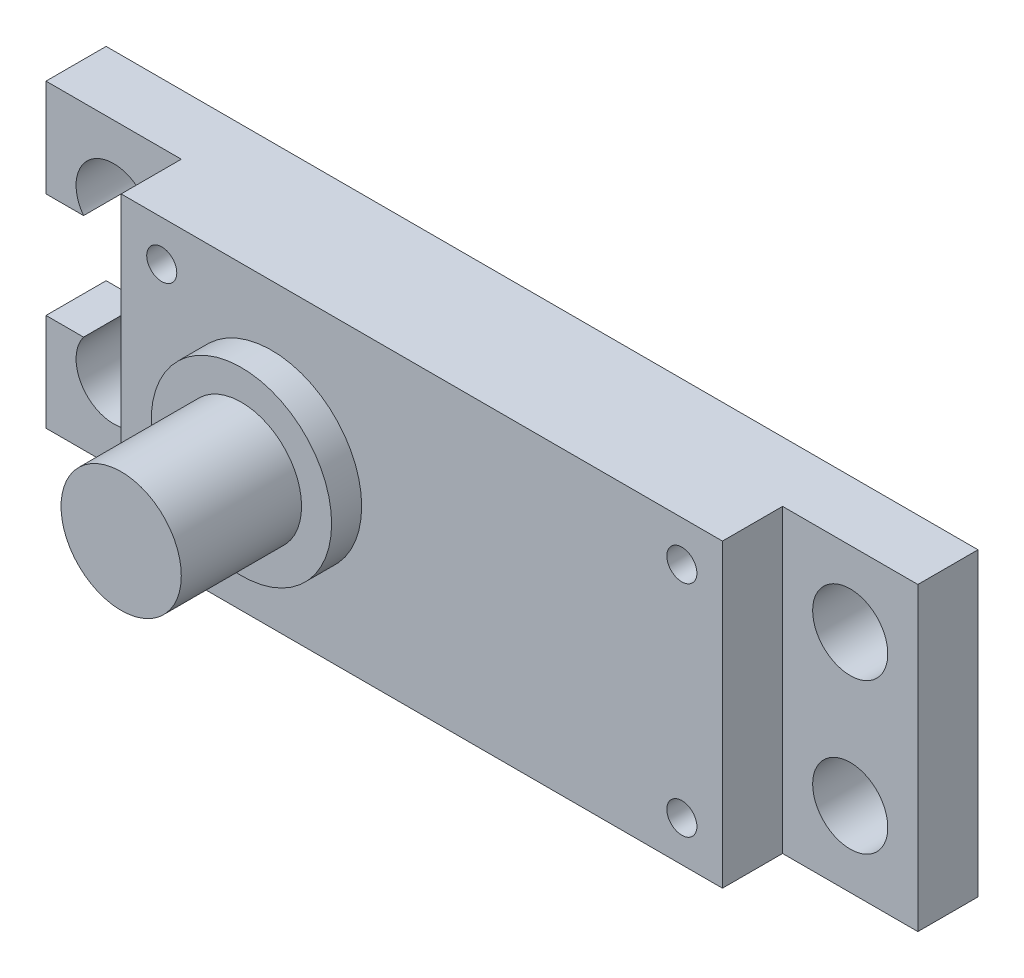
SolidWorks part; units mm, degrees
ref_plane "Face" through (0, 0, 0) normal (0, 0, 1) x (1, 0, 0)
ref_plane "Dessus" through (0, 0, 0) normal (0, 1, 0) x (1, 0, 0)
ref_plane "Droite" through (0, 0, 0) normal (1, 0, 0) x (0, 0, -1)
sketch "Esquisse1" plane through (0, 0, 0) normal (0, 0, 1) x (1, 0, 0)
  line L1 (0, 20) -> (58, 20)
  line L2 (0, 20) -> (0, 0)
  line L3 (0, 0) -> (58, 0)
  line L4 (58, 20) -> (58, 0)
  dimension "D1" = 20
  dimension "D2" = 58
extrude "Extrusion1" add sketch "Esquisse1" along normal blind 8
sketch "Esquisse2" plane through (0, 0, 0) normal (0, 0, -1) x (-1, 0, 0)
  line L0 (-60.8088, 10) -> (3.3885, 10) construction
  line L1 (-47.7, 18.7) -> (-10.3, 18.7)
  line L2 (-47.7, 18.7) -> (-47.7, 1.3)
  line L3 (-47.7, 1.3) -> (-10.3, 1.3)
  line L4 (-10.3, 18.7) -> (-10.3, 1.3)
  line L5 (-29, 26.2419) -> (-29, -6.2687) construction
  line L6 (-58, 0) -> (-58, 20) construction
  line L7 (0, 20) -> (0, 0) construction
  line L8 (-58, 20) -> (0, 20) construction
  line L9 (0, 0) -> (-58, 0) construction
  dimension "D1" = 37.4
  dimension "D2" = 17.4
extrude "Enlèv. mat.-Extru.1" cut sketch "Esquisse2" against normal blind 6
sketch "Esquisse3" plane through (0, 20, 0) normal (0, 1, 0) x (1, 0, 0)
  line L0 (29, 7.8921) -> (29, -24.2537) construction
  line L1 (58, -8) -> (58, 0) construction
  line L2 (0, -8) -> (0, 0) construction
  line L3 (58, 0) -> (0, 0) construction
  line L4 (9, -4) -> (0, -4)
  line L5 (9, -4) -> (9, -8)
  line L6 (9, -8) -> (0, -8)
  line L7 (0, -4) -> (0, -8)
  line L8 (58, -4) -> (58, -8)
  line L9 (49, -8) -> (58, -8)
  line L10 (49, -4) -> (49, -8)
  line L11 (49, -4) -> (58, -4)
  dimension "D1" = 4
  dimension "D2" = 40
extrude "Enlèv. mat.-Extru.2" cut sketch "Esquisse3" against normal through all
sketch "Esquisse4" plane through (0, 0, 0) normal (0, 0, -1) x (-1, 0, 0)
  line L0 (-29, 25.2889) -> (-29, -5.3683) construction
  line L1 (-64.7005, 10) -> (4.5905, 10) construction
  line L2 (0, 20) -> (0, 0) construction
  line L3 (-58, 0) -> (-58, 20) construction
  line L4 (-58, 20) -> (0, 20) construction
  line L5 (0, 0) -> (-58, 0) construction
  line L6 (-49, 0) -> (-49, 20) construction
  circle A0 centre (-53.5, 15) radius 2.5
  circle A1 centre (-46.3, 17.3) radius 1
  circle A2 centre (-46.3, 2.7) radius 1
  circle A3 centre (-53.5, 5) radius 2.5
  circle A4 centre (-4.5, 5) radius 2.5
  circle A5 centre (-11.7, 2.7) radius 1
  circle A6 centre (-11.7, 17.3) radius 1
  circle A7 centre (-4.5, 15) radius 2.5
  dimension "D1" = 5
  dimension "D2" = 2
  dimension "D3" = 4.5
  dimension "D4" = 2.7
  dimension "D5" = 10
  dimension "D6" = 14.6
extrude "Enlèv. mat.-Extru.3" cut sketch "Esquisse4" against normal through all
sketch "Esquisse5" plane through (0, 0, 8) normal (0, 0, 1) x (1, 0, 0)
  line L0 (3.4324, 10) -> (55.7935, 10) construction
  line L1 (9, 0) -> (49, 0) construction
  line L2 (49, 20) -> (9, 20) construction
  line L3 (9, 0) -> (9, 20) construction
  circle A0 centre (19, 10) radius 4
  dimension "D1" = 8
  dimension "D2" = 10
extrude "Extrusion2" add sketch "Esquisse5" along normal blind 10
sketch "Esquisse6" plane through (0, 0, 0) normal (0, 0, -1) x (-1, 0, 0)
  line L0 (-28.8333, 10) -> (7.867, 10) construction
  line L1 (-58, 20) -> (0, 20) construction
  line L2 (0, 0) -> (-58, 0) construction
  line L3 (0, 20) -> (0, 0) construction
  line L4 (-10.3, 13.5) -> (0, 13.5)
  line L5 (-10.3, 13.5) -> (-10.3, 6.5)
  line L6 (-10.3, 6.5) -> (0, 6.5)
  line L7 (0, 13.5) -> (0, 6.5)
  line L8 (-10.3, 1.3) -> (-10.3, 18.7) construction
  dimension "D1" = 7
extrude "Enlèv. mat.-Extru.4" cut sketch "Esquisse6" against normal up to surface (4 mm away) up to face at (2, 15, 4)
sketch "Esquisse10" plane through (0, 20, 0) normal (0, 1, 0) x (1, 0, 0)
  line L0 (10.3, -6) -> (47.7, -6) construction
  line L1 (10.3, -6) -> (47.7, -6)
  line L2 (10.3, -6) -> (10.3, -6.5)
  line L3 (10.3, -6.5) -> (47.7, -6.5)
  line L4 (47.7, -6) -> (47.7, -6.5)
  line L5 (47.7, -6) -> (47.7, 0) construction
  line L6 (10.3, -6) -> (10.3, 0) construction
  dimension "D1" = 0.5
extrude "Extrusion8" add sketch "Esquisse10" against normal up to surface (20 mm away) up to face at (29, 0, 4)
sketch "Esquisse8" plane through (0, 0, 0) normal (0, 0, -1) x (-1, 0, 0)
  line L0 (-62.3972, 10) -> (5.8306, 10) construction
  line L1 (-29, 26.3213) -> (-29, -7.751) construction
  line L2 (-58, 0) -> (-58, 20) construction
  line L3 (0, 20) -> (0, 13.5) construction
  line L4 (-58, 20) -> (0, 20) construction
  line L5 (0, 0) -> (-58, 0) construction
  line L6 (-25.3068, 17.7) -> (-25.3068, 2.3)
  line L7 (-46.9892, 17.7) -> (-43.9892, 17.7)
  line L8 (-46.9892, 17.7) -> (-46.9892, 2.3)
  line L9 (-46.9892, 2.3) -> (-43.9892, 2.3)
  line L10 (-43.9892, 17.7) -> (-43.9892, 2.3)
  line L11 (-41.5885, 17.7) -> (-38.5885, 17.7)
  line L12 (-41.5885, 17.7) -> (-41.5885, 2.3)
  line L13 (-41.5885, 2.3) -> (-38.5885, 2.3)
  line L14 (-38.5885, 17.7) -> (-38.5885, 2.3)
  line L15 (-35.6932, 17.7) -> (-32.6932, 17.7)
  line L16 (-35.6932, 17.7) -> (-35.6932, 2.3)
  line L17 (-35.6932, 2.3) -> (-32.6932, 2.3)
  line L18 (-32.6932, 17.7) -> (-32.6932, 2.3)
  line L19 (-30.5, 17.7) -> (-27.5, 17.7)
  line L20 (-30.5, 17.7) -> (-30.5, 2.3)
  line L21 (-30.5, 2.3) -> (-27.5, 2.3)
  line L22 (-27.5, 17.7) -> (-27.5, 2.3)
  line L23 (-22.3068, 2.3) -> (-25.3068, 2.3)
  line L24 (-22.3068, 17.7) -> (-22.3068, 2.3)
  line L25 (-22.3068, 17.7) -> (-25.3068, 17.7)
  line L26 (-19.4115, 17.7) -> (-19.4115, 2.3)
  line L27 (-16.4115, 2.3) -> (-19.4115, 2.3)
  line L28 (-16.4115, 17.7) -> (-16.4115, 2.3)
  line L29 (-16.4115, 17.7) -> (-19.4115, 17.7)
  line L30 (-14.0108, 17.7) -> (-14.0108, 2.3)
  line L31 (-11.0108, 2.3) -> (-14.0108, 2.3)
  line L32 (-11.0108, 17.7) -> (-11.0108, 2.3)
  line L33 (-11.0108, 17.7) -> (-14.0108, 17.7)
  line L34 (-10.3, 18.7) -> (-47.7, 18.7) construction
  dimension "D1" = 3
  dimension "D2" = 1
extrude "Extrusion7" add sketch "Esquisse8" against normal up to surface (6.5 mm away) draft 9
sketch "Esquisse11" plane through (0, 0, 8) normal (0, 0, 1) x (1, 0, 0)
  circle A0 centre (19, 10) radius 6
  circle A1 centre (19, 10) radius 4 construction
  dimension "D1" = 12
extrude "Extrusion9" add sketch "Esquisse11" along normal blind 2
